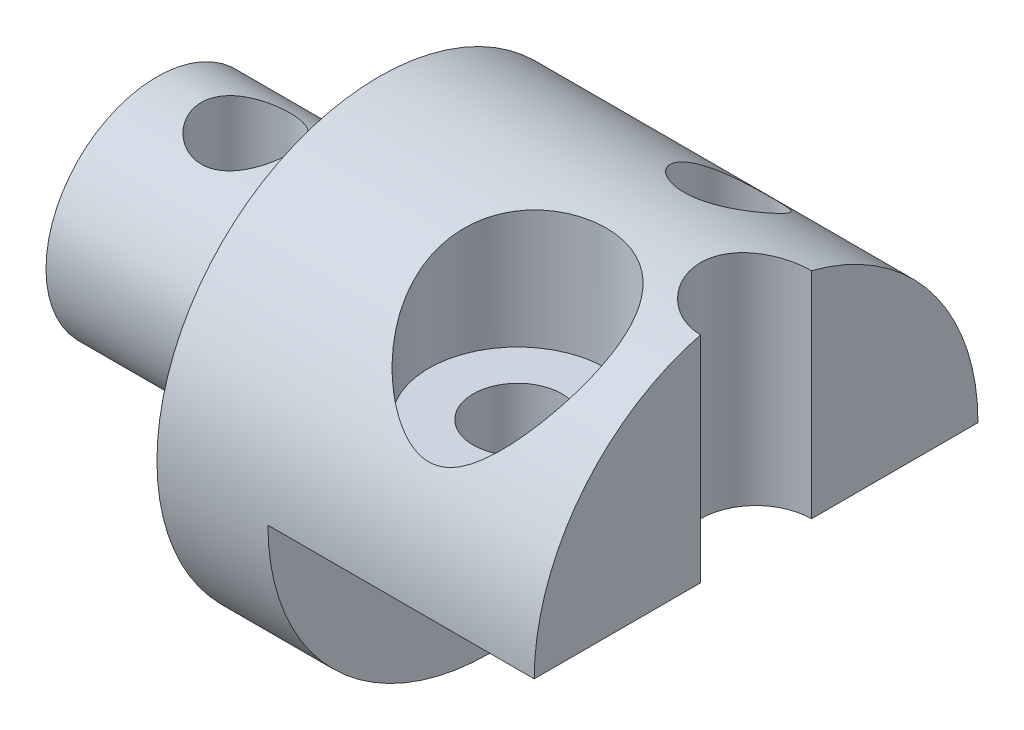
SolidWorks part; units mm, degrees
material "1.0037 (S235JR)"
ref_plane "Płaszczyzna XY" through (0, 0, 0) normal (0, 0, 1) x (1, 0, 0)
ref_plane "Płaszczyzna XZ" through (0, 0, 0) normal (0, 1, 0) x (1, 0, 0)
ref_plane "Płaszczyzna YZ" through (0, 0, 0) normal (1, 0, 0) x (0, 0, -1)
sketch "Szkic1" plane through (0, 0, 0) normal (0, 1, 0) x (1, 0, 0)
  line L1 (2.5, -0.875) -> (2.5, 9.125)
  line L2 (2.5, 9.125) -> (-2.5, 9.125)
  line L6 (-2.5, 9.125) -> (-2.5, 4.125)
  line L7 (-2.5, 4.125) -> (-12.5, 4.125)
  line L8 (-12.5, 4.125) -> (-12.5, -0.875)
  line L9 (-12.5, -0.875) -> (2.5, -0.875)
  line L10 (2.5, 9.125) -> (2.5, -10.875) construction
  dimension "D1" = 5
  dimension "D2" = 10
  dimension "D3" = 5
  dimension "D4" = 10
revolve "Obrót1" add sketch "Szkic1" angle 360 about L9
sketch "Szkic2" plane through (2.5, 0, 0) normal (1, 0, 0) x (0, 0, -1)
  line L0 (-10.875, 0) -> (9.125, 0)
  circle A0 centre (-0.875, 0) radius 10 construction
  arc A1 (9.125, 0) -> (-10.875, 0) centre (-0.875, 0) ccw
extrude "Dodanie-wyciągnięcie1" add sketch "Szkic2" along normal blind 12
ref_plane "Płaszczyzna1" through (0, 0, 0) normal (0, -1, 0) x (-1, 0, 0)
sketch "Szkic3" plane through (0, 0, 0) normal (0, -1, 0) x (-1, 0, 0)
  line L0 (-2.5, -10.875) -> (-2.5, 9.125) construction
  line L1 (-2.5, -10.875) -> (2.5, -10.875) construction
  line L2 (-14.5, 9.125) -> (-2.5, 9.125) construction
  line L3 (-2.5, -10.375) -> (-14.5, -0.875)
  line L4 (-14.5, 9.125) -> (-14.5, -10.875) construction
  line L5 (-14.5, -0.875) -> (-2.5, 8.625)
  line L6 (-8.5, -10.875) -> (-8.5, 9.125)
  line L7 (-14.5, -10.875) -> (-2.5, -10.875) construction
  circle A0 centre (-8.5, -5.625) radius 2
  circle A1 centre (-8.5, 3.875) radius 2
  point P0 (-2.5, -10.375)
  point P1 (-2.5, 8.625)
  dimension "D1" = 0.5
  dimension "D2" = 0.5
extrude "Wytnij-wyciągnięcie1" cut sketch "Szkic3" against normal blind 12 contours A1 | A0
ref_plane "Płaszczyzna2" through (0, 4.5, 0) normal (0, -1, 0) x (-1, 0, 0)
sketch "Szkic5" plane through (0, 4.5, 0) normal (0, -1, 0) x (-1, 0, 0)
  circle A0 centre (-8.5, -5.625) radius 4
extrude "Wytnij-wyciągnięcie4" cut sketch "Szkic5" against normal blind 10 contours A0
ref_plane "Płaszczyzna3" through (14.5, 0, 0) normal (1, 0, 0) x (0, 0, -1)
sketch "Szkic7" plane through (-12.5, 0, 0) normal (-1, 0, 0) x (0, 0, 1)
  circle A0 centre (0.875, 0) radius 2
  circle A1 centre (0.875, 0) radius 5
  circle A2 centre (0.875, 0) radius 5
  dimension "D1" = 0
sketch "Szkic8" plane through (0, 0, 0) normal (0, 0, 1) x (1, 0, 0)
  line L0 (-6.6, 0) -> (6.6, 0) construction
  line L1 (14.5, -5.5) -> (14.5, 5.5) construction
  circle A0 centre (12.5, 0) radius 2
  point P0 (12.5, 0)
  dimension "D1" = 2
ref_plane "Płaszczyzna4" through (0, 0, 0.88) normal (0, 0, 1) x (1, 0, 0)
sketch "Szkic10" plane through (0, 0, 0.88) normal (0, 0, 1) x (1, 0, 0)
  line L0 (-6.6, 0) -> (6.6, 0) construction
  circle A0 centre (14.5, 0) radius 2
  circle A1 centre (12.5, 0) radius 2 construction
sketch "Szkic12" plane through (0, 0, 0) normal (0, 1, 0) x (1, 0, 0)
  line L0 (12.5, -0.88) -> (16.5, -0.88) construction
  circle A0 centre (14.5, -0.88) radius 2.5
extrude "Wytnij-wyciągnięcie8" cut sketch "Szkic12" along normal through all
ref_plane "Płaszczyzna5" through (0, 14.5, 0) normal (0, 1, 0) x (1, 0, 0)
sketch "Szkic13" plane through (0, 14.5, 0) normal (0, 1, 0) x (1, 0, 0)
  line L0 (-2.5, -0.875) -> (-12.5, -0.875) construction
  line L1 (-2.5, -0.875) -> (-8.5, -0.875) construction
  line L2 (-2.5, 9.125) -> (-2.5, -10.875) construction
  circle A0 centre (-8.5, -0.875) radius 2
  dimension "D1" = 6
extrude "Wytnij-wyciągnięcie9" cut sketch "Szkic13" against normal through all contours A0
